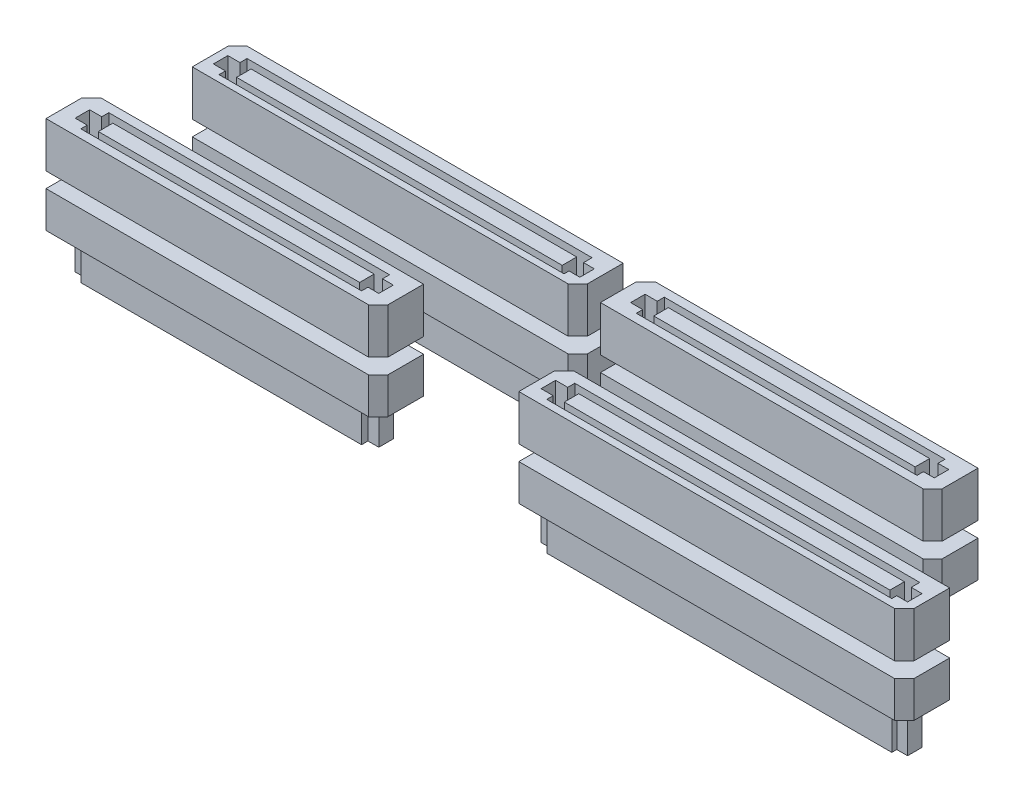
SolidWorks part; units mm, degrees
ref_plane "Front Plane" through (0, 0, 0) normal (0, 0, 1) x (1, 0, 0)
ref_plane "Top Plane" through (0, 0, 0) normal (0, 1, 0) x (1, 0, 0)
ref_plane "Right Plane" through (0, 0, 0) normal (1, 0, 0) x (0, 0, -1)
ref_plane "Plane1" through (0, -1.6866, 0) normal (0, 1, 0) x (1, 0, 0)
ref_plane "center-of-slot" through (0, -0.8433, 0) normal (0, 1, 0) x (1, 0, 0)
sketch "Sketch1" plane through (0, 0, 0) normal (0, 1, 0) x (1, 0, 0)
  line L0 (55.811, 9.5) -> (97.25, 9.5)
  line L1 (3.686, 9.5) -> (39.25, 9.5)
  line L2 (2.625, 8.439) -> (2.625, 4.5)
  line L3 (2.625, 4.5) -> (39.25, 4.5) construction
  line L4 (39.25, 9.5) -> (39.25, 4.5) construction
  line L5 (0, 0) -> (100, 0) construction
  line L6 (0, 0) -> (0, 75) construction
  line L7 (0, 75) -> (100, 75) construction
  line L8 (100, 0) -> (100, 75) construction
  line L9 (54.75, 8.439) -> (54.75, 4.5)
  line L10 (54.75, 4.5) -> (97.25, 4.5) construction
  line L11 (97.25, 9.5) -> (97.25, 4.5) construction
  line L12 (51.811, 22.5) -> (87.375, 22.5)
  line L13 (6.811, 22.5) -> (48.25, 22.5)
  line L14 (5.75, 21.439) -> (5.75, 17.5)
  line L15 (5.75, 17.5) -> (48.25, 17.5) construction
  line L16 (48.25, 22.5) -> (48.25, 17.5) construction
  line L17 (50.75, 21.439) -> (50.75, 17.5)
  line L18 (50.75, 17.5) -> (87.375, 17.5) construction
  line L19 (87.375, 22.5) -> (87.375, 17.5) construction
  line L20 (5.75, 21.439) -> (6.811, 22.5)
  line L21 (50.75, 21.439) -> (51.811, 22.5)
  line L22 (54.75, 8.439) -> (55.811, 9.5)
  line L23 (2.625, 8.439) -> (3.686, 9.5)
  line L24 (2.625, 4.5) -> (38.195, 4.5)
  line L25 (38.195, 4.5) -> (39.25, 5.555)
  line L26 (39.25, 5.555) -> (39.25, 9.5)
  line L27 (50.75, 17.5) -> (86.32, 17.5)
  line L28 (86.32, 17.5) -> (87.375, 18.555)
  line L29 (87.375, 18.555) -> (87.375, 22.5)
  line L30 (54.75, 4.5) -> (96.19, 4.5)
  line L31 (96.19, 4.5) -> (97.25, 5.56)
  line L32 (97.25, 5.56) -> (97.25, 9.5)
  line L33 (5.75, 17.5) -> (47.19, 17.5)
  line L34 (47.19, 17.5) -> (48.25, 18.56)
  line L35 (48.25, 18.56) -> (48.25, 22.5)
  point P0 (2.625, 9.5)
  point P9 (54.75, 9.5)
  point P13 (5.75, 22.5)
  point P17 (50.75, 22.5)
extrude "SV" add sketch "Sketch1" along normal blind 5
sketch "Sketch3" plane through (0, 5, 0) normal (0, 1, 0) x (1, 0, 0)
  line L0 (4.1893, 7.7457) -> (5.5243, 7.7457)
  line L1 (4.1893, 8.5242) -> (37.667, 8.5242) construction
  line L2 (4.1893, 8.5242) -> (4.1893, 5.4386) construction
  line L3 (4.1893, 5.4386) -> (37.667, 5.4386) construction
  line L4 (37.667, 8.5242) -> (37.667, 5.4386) construction
  line L5 (5.5243, 7.7457) -> (5.5243, 8.5242)
  line L6 (5.5243, 8.5242) -> (36.4757, 8.5242)
  line L7 (36.4757, 8.5242) -> (36.4757, 7.7457)
  line L8 (36.4757, 7.7457) -> (37.667, 7.7457)
  line L9 (37.667, 7.7457) -> (37.667, 6.1479)
  line L10 (37.667, 6.1479) -> (36.4757, 6.1479)
  line L11 (36.4757, 6.1479) -> (36.4757, 5.4386)
  line L12 (36.4757, 5.4386) -> (5.5243, 5.4386)
  line L13 (5.5243, 5.4386) -> (5.5243, 6.1479)
  line L14 (5.5243, 6.1479) -> (4.1893, 6.1479)
  line L15 (4.1893, 6.1479) -> (4.1893, 7.7457)
  line L16 (52.4211, 20.7536) -> (53.7561, 20.7536)
  line L17 (6.7471, 7.7457) -> (35.5588, 7.7457)
  line L18 (6.7471, 7.7457) -> (6.7471, 6.1479)
  line L19 (6.7471, 6.1479) -> (35.5588, 6.1479)
  line L20 (35.5588, 7.7457) -> (35.5588, 6.1479)
  line L21 (52.4211, 21.532) -> (85.8988, 21.532) construction
  line L22 (52.4211, 21.532) -> (52.4211, 18.4464) construction
  line L23 (52.4211, 18.4464) -> (85.8988, 18.4464) construction
  line L24 (85.8988, 21.532) -> (85.8988, 18.4464) construction
  line L25 (53.7561, 20.7536) -> (53.7561, 21.532)
  line L26 (53.7561, 21.532) -> (84.7075, 21.532)
  line L27 (84.7075, 21.532) -> (84.7075, 20.7536)
  line L28 (84.7075, 20.7536) -> (85.8988, 20.7536)
  line L29 (85.8988, 20.7536) -> (85.8988, 19.1558)
  line L30 (85.8988, 19.1558) -> (84.7075, 19.1558)
  line L31 (84.7075, 19.1558) -> (84.7075, 18.4464)
  line L32 (84.7075, 18.4464) -> (53.7561, 18.4464)
  line L33 (53.7561, 18.4464) -> (53.7561, 19.1558)
  line L34 (53.7561, 19.1558) -> (52.4211, 19.1558)
  line L35 (52.4211, 19.1558) -> (52.4211, 20.7536)
  line L36 (54.9789, 20.7536) -> (83.7906, 20.7536)
  line L37 (54.9789, 20.7536) -> (54.9789, 19.1558)
  line L38 (54.9789, 19.1558) -> (83.7906, 19.1558)
  line L39 (83.7906, 20.7536) -> (83.7906, 19.1558)
  line L40 (55.7059, 7.599) -> (57.0409, 7.599)
  line L41 (55.7059, 8.3775) -> (96.2696, 8.3775) construction
  line L42 (55.7059, 8.3775) -> (55.7059, 5.2919) construction
  line L43 (55.7059, 5.2919) -> (96.2696, 5.2919) construction
  line L44 (96.2696, 8.3775) -> (96.2696, 5.2919) construction
  line L45 (57.0409, 7.599) -> (57.0409, 8.3775)
  line L46 (57.0409, 8.3775) -> (95.0783, 8.3775)
  line L47 (95.0783, 8.3775) -> (95.0783, 7.4377)
  line L48 (95.0783, 7.4377) -> (96.2696, 7.4377)
  line L49 (96.2696, 7.4377) -> (96.2696, 5.8399)
  line L50 (96.2696, 5.8399) -> (95.0783, 5.8399)
  line L51 (95.0783, 5.8399) -> (95.0783, 5.2919)
  line L52 (95.0783, 5.2919) -> (57.0409, 5.2919)
  line L53 (57.0409, 5.2919) -> (57.0409, 6.0012)
  line L54 (57.0409, 6.0012) -> (55.7059, 6.0012)
  line L55 (55.7059, 6.0012) -> (55.7059, 7.599)
  line L56 (58.2637, 7.599) -> (94.1615, 7.599)
  line L57 (58.2637, 7.599) -> (58.2637, 6.0012)
  line L58 (58.2637, 6.0012) -> (94.1615, 6.0012)
  line L59 (94.1615, 7.599) -> (94.1615, 6.0012)
  line L60 (6.6366, 20.5397) -> (7.9716, 20.5397)
  line L61 (6.6366, 21.3182) -> (47.2003, 21.3182) construction
  line L62 (6.6366, 21.3182) -> (6.6366, 18.2325) construction
  line L63 (6.6366, 18.2325) -> (47.2003, 18.2325) construction
  line L64 (47.2003, 21.3182) -> (47.2003, 18.2325) construction
  line L65 (7.9716, 20.5397) -> (7.9716, 21.3182)
  line L66 (7.9716, 21.3182) -> (46.009, 21.3182)
  line L67 (46.009, 21.3182) -> (46.009, 20.3784)
  line L68 (46.009, 20.3784) -> (47.2003, 20.3784)
  line L69 (47.2003, 20.3784) -> (47.2003, 18.7806)
  line L70 (47.2003, 18.7806) -> (46.009, 18.7806)
  line L71 (46.009, 18.7806) -> (46.009, 18.2325)
  line L72 (46.009, 18.2325) -> (7.9716, 18.2325)
  line L73 (7.9716, 18.2325) -> (7.9716, 18.9419)
  line L74 (7.9716, 18.9419) -> (6.6366, 18.9419)
  line L75 (6.6366, 18.9419) -> (6.6366, 20.5397)
  line L76 (9.1944, 20.5397) -> (45.0922, 20.5397)
  line L77 (9.1944, 20.5397) -> (9.1944, 18.9419)
  line L78 (9.1944, 18.9419) -> (45.0922, 18.9419)
  line L79 (45.0922, 20.5397) -> (45.0922, 18.9419)
extrude "Cut-Extrude1" cut sketch "Sketch3" against normal blind 4
sketch "Sketch6" plane through (0, -1.6866, 0) normal (0, 1, 0) x (1, 0, 0)
  line L0 (2.625, 4.5) -> (2.625, 9.5) construction
  line L1 (5.75, 22.5) -> (48.25, 22.5) construction
  line L2 (5.75, 22.5) -> (5.75, 17.5) construction
  line L3 (5.75, 17.5) -> (48.25, 17.5) construction
  line L4 (48.25, 22.5) -> (48.25, 17.5) construction
  line L5 (50.75, 22.5) -> (87.375, 22.5) construction
  line L6 (50.75, 22.5) -> (50.75, 17.5) construction
  line L7 (50.75, 17.5) -> (87.375, 17.5) construction
  line L8 (87.375, 22.5) -> (87.375, 17.5) construction
  line L9 (97.25, 9.5) -> (54.75, 9.5) construction
  line L10 (97.25, 9.5) -> (97.25, 4.5) construction
  line L11 (97.25, 4.5) -> (54.75, 4.5) construction
  line L12 (54.75, 9.5) -> (54.75, 4.5) construction
  line L13 (39.25, 9.5) -> (2.625, 9.5) construction
  line L14 (39.25, 9.5) -> (39.25, 4.5) construction
  line L15 (39.25, 4.5) -> (2.625, 4.5) construction
  line L16 (2.625, 9.5) -> (2.625, 4.5) construction
  line L17 (2.625, 4.5) -> (38.195, 4.5)
  line L18 (2.625, 9.5) -> (39.25, 9.5) construction
  line L19 (48.25, 18.5619) -> (47.1881, 17.5)
  line L20 (39.25, 5.555) -> (39.25, 9.5)
  line L21 (48.25, 18.5619) -> (48.25, 22.5)
  line L22 (47.1881, 17.5) -> (5.75, 17.5)
  line L23 (39.25, 5.555) -> (38.195, 4.5)
  line L24 (54.75, 4.5) -> (96.19, 4.5)
  line L25 (96.19, 4.5) -> (97.25, 5.56)
  line L26 (97.25, 5.56) -> (97.25, 9.5)
  line L27 (50.75, 17.5) -> (86.32, 17.5)
  line L28 (86.32, 17.5) -> (87.375, 18.555)
  line L29 (87.375, 18.555) -> (87.375, 22.5)
  line L30 (2.625, 4.5) -> (2.625, 8.44)
  line L31 (2.625, 8.44) -> (3.685, 9.5)
  line L32 (3.685, 9.5) -> (39.25, 9.5)
  line L33 (5.75, 17.5) -> (5.75, 21.44)
  line L34 (5.75, 21.44) -> (6.81, 22.5)
  line L35 (6.81, 22.5) -> (48.25, 22.5)
  line L36 (54.75, 4.5) -> (54.75, 8.44)
  line L37 (54.75, 8.44) -> (55.81, 9.5)
  line L38 (55.81, 9.5) -> (97.25, 9.5)
  line L39 (87.375, 22.5) -> (51.805, 22.5)
  line L40 (51.805, 22.5) -> (50.75, 21.445)
  line L41 (50.75, 21.445) -> (50.75, 17.5)
  point P0 (5.75, 22.5)
  point P6 (50.75, 22.5)
  point P15 (54.75, 9.5)
extrude "SV4(a)" add sketch "Sketch6" against normal blind 4 separate body
sketch "Sketch7" plane through (0, -5.6866, 0) normal (0, -1, 0) x (1, 0, 0)
  line L0 (7.9716, -21.3182) -> (7.9716, -20.5397)
  line L1 (7.9716, -20.5397) -> (6.6366, -20.5397)
  line L2 (6.6366, -20.5397) -> (6.6366, -18.9419)
  line L3 (6.6366, -18.9419) -> (7.9716, -18.9419)
  line L4 (7.9716, -18.9419) -> (7.9716, -18.2325)
  line L6 (7.9716, -18.2325) -> (46.009, -18.2325)
  line L7 (46.009, -18.2325) -> (46.009, -18.7806)
  line L8 (46.009, -18.7806) -> (47.2003, -18.7806)
  line L9 (47.2003, -18.7806) -> (47.2003, -20.3784)
  line L10 (47.2003, -20.3784) -> (46.009, -20.3784)
  line L11 (46.009, -20.3784) -> (46.009, -21.3182)
  line L12 (46.009, -21.3182) -> (7.9716, -21.3182)
  line L13 (53.7561, -21.532) -> (84.7075, -21.532)
  line L14 (9.1944, -20.5397) -> (45.0922, -20.5397)
  line L15 (9.1944, -20.5397) -> (9.1944, -18.9419)
  line L16 (9.1944, -18.9419) -> (45.0922, -18.9419)
  line L17 (45.0922, -20.5397) -> (45.0922, -18.9419)
  line L18 (54.9789, -20.7536) -> (83.7906, -20.7536)
  line L19 (54.9789, -20.7536) -> (54.9789, -19.1558)
  line L20 (54.9789, -19.1558) -> (83.7906, -19.1558)
  line L21 (83.7906, -20.7536) -> (83.7906, -19.1558)
  line L22 (94.1615, -7.599) -> (58.2637, -7.599)
  line L23 (94.1615, -7.599) -> (94.1615, -6.0012)
  line L24 (94.1615, -6.0012) -> (58.2637, -6.0012)
  line L25 (58.2637, -7.599) -> (58.2637, -6.0012)
  line L26 (35.5588, -7.7457) -> (6.7471, -7.7457)
  line L27 (35.5588, -7.7457) -> (35.5588, -6.1479)
  line L28 (35.5588, -6.1479) -> (6.7471, -6.1479)
  line L29 (6.7471, -7.7457) -> (6.7471, -6.1479)
  line L30 (84.7075, -21.532) -> (84.7075, -20.7536)
  line L31 (84.7075, -20.7536) -> (85.8988, -20.7536)
  line L32 (85.8988, -20.7536) -> (85.8988, -19.1558)
  line L33 (85.8988, -19.1558) -> (84.7075, -19.1558)
  line L34 (84.7075, -19.1558) -> (84.7075, -18.4464)
  line L35 (84.7075, -18.4464) -> (53.7561, -18.4464)
  line L36 (53.7561, -18.4464) -> (53.7561, -19.1558)
  line L37 (53.7561, -19.1558) -> (52.4211, -19.1558)
  line L38 (52.4211, -19.1558) -> (52.4211, -20.7536)
  line L39 (52.4211, -20.7536) -> (53.7561, -20.7536)
  line L40 (53.7561, -20.7536) -> (53.7561, -21.532)
  line L41 (57.0409, -8.3775) -> (57.0409, -7.599)
  line L42 (57.0409, -7.599) -> (55.7059, -7.599)
  line L43 (55.7059, -7.599) -> (55.7059, -6.0012)
  line L44 (55.7059, -6.0012) -> (57.0409, -6.0012)
  line L45 (57.0409, -6.0012) -> (57.0409, -5.2919)
  line L46 (57.0409, -5.2919) -> (95.0783, -5.2919)
  line L47 (95.0783, -5.2919) -> (95.0783, -5.8399)
  line L48 (95.0783, -5.8399) -> (96.2696, -5.8399)
  line L49 (96.2696, -5.8399) -> (96.2696, -7.4377)
  line L50 (96.2696, -7.4377) -> (95.0783, -7.4377)
  line L51 (95.0783, -7.4377) -> (95.0783, -8.3775)
  line L52 (95.0783, -8.3775) -> (57.0409, -8.3775)
  line L53 (4.1893, -6.1479) -> (5.5243, -6.1479)
  line L54 (5.5243, -6.1479) -> (5.5243, -5.4386)
  line L55 (5.5243, -5.4386) -> (36.4757, -5.4386)
  line L56 (36.4757, -5.4386) -> (36.4757, -6.1479)
  line L57 (36.4757, -6.1479) -> (37.667, -6.1479)
  line L58 (37.667, -6.1479) -> (37.667, -7.7457)
  line L59 (37.667, -7.7457) -> (36.4757, -7.7457)
  line L60 (36.4757, -7.7457) -> (36.4757, -8.5242)
  line L61 (36.4757, -8.5242) -> (5.5243, -8.5242)
  line L62 (5.5243, -8.5242) -> (5.5243, -7.7457)
  line L63 (5.5243, -7.7457) -> (4.1893, -7.7457)
  line L64 (4.1893, -7.7457) -> (4.1893, -6.1479)
extrude "SV4(b)" add sketch "Sketch7" along normal blind 4
